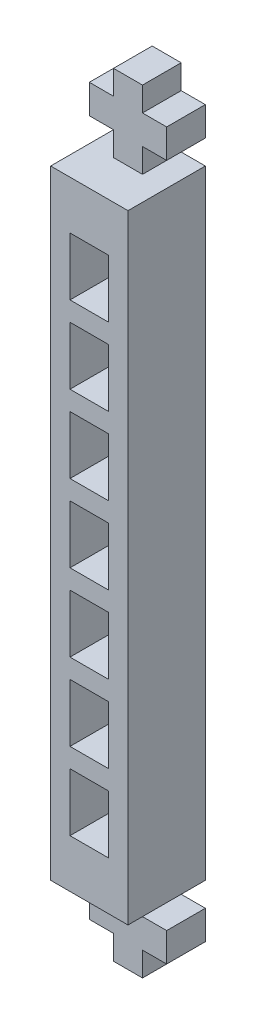
SolidWorks part; units mm, degrees
ref_plane "Front Plane" through (0, 0, 0) normal (0, 0, 1) x (1, 0, 0)
ref_plane "Top Plane" through (0, 0, 0) normal (0, 1, 0) x (1, 0, 0)
ref_plane "Right Plane" through (0, 0, 0) normal (1, 0, 0) x (0, 0, -1)
sketch "Sketch1" plane through (0, 0, 0) normal (0, 1, 0) x (1, 0, 0)
  line L1 (0, 0) -> (20, 0)
  line L2 (0, 0) -> (0, 20)
  line L3 (0, 20) -> (20, 20)
  line L4 (20, 0) -> (20, 20)
  dimension "D1" = 20
  dimension "D2" = 20
extrude "Boss-Extrude1" add sketch "Sketch1" along normal blind 200
sketch "Sketch2" plane through (20, 0, 0) normal (1, 0, 0) x (0, 0, -1)
  line L1 (0, 200) -> (10, 200)
  line L2 (0, 200) -> (0, 180)
  line L3 (0, 180) -> (10, 180)
  line L4 (10, 200) -> (10, 180)
  line L5 (0, 0) -> (10, 0)
  line L6 (0, 0) -> (0, 20)
  line L7 (0, 20) -> (10, 20)
  line L8 (10, 0) -> (10, 20)
  dimension "D1" = 20
  dimension "D2" = 10
  dimension "D3" = 20
  dimension "D4" = 10
extrude "Cut-Extrude1" cut sketch "Sketch2" against normal through all
sketch "Sketch3" plane through (0, 0, -20) normal (0, 0, -1) x (-1, 0, 0)
  line L1 (-20, 200) -> (0, 200)
  line L2 (-20, 200) -> (-20, 180)
  line L3 (-20, 180) -> (0, 180)
  line L4 (0, 200) -> (0, 180)
  line L5 (-20, 200) -> (-13.75, 200)
  line L6 (-20, 200) -> (-20, 193.75)
  line L7 (-20, 193.75) -> (-13.75, 193.75)
  line L8 (-13.75, 200) -> (-13.75, 193.75)
  line L9 (0, 200) -> (-6.25, 200)
  line L10 (0, 200) -> (0, 193.75)
  line L11 (0, 193.75) -> (-6.25, 193.75)
  line L12 (-6.25, 200) -> (-6.25, 193.75)
  line L13 (0, 180) -> (-6.25, 180)
  line L14 (0, 180) -> (0, 186.25)
  line L15 (0, 186.25) -> (-6.25, 186.25)
  line L16 (-6.25, 180) -> (-6.25, 186.25)
  line L17 (-20, 180) -> (-13.75, 180)
  line L18 (-20, 180) -> (-20, 186.25)
  line L19 (-20, 186.25) -> (-13.75, 186.25)
  line L20 (-13.75, 180) -> (-13.75, 186.25)
  line M22 (0, 0) -> (0, 200)
  line M23 (0, 200) -> (-20, 200)
  line M24 (-20, 200) -> (-20, 0)
  dimension "D1" = 20
  dimension "D2" = 20
  dimension "D3" = 6.25
extrude "Cut-Extrude2" cut sketch "Sketch3" against normal through all contours L12 L11 L4 M23 | L8 L1 L7 M24 | L3 L20 L19 M24 | L16 L3 L15 M22
sketch "Sketch4" plane through (0, 0, -20) normal (0, 0, -1) x (-1, 0, 0)
  line L0 (0, 180) -> (0, 0) construction
  line L1 (-20, 0) -> (0, 0)
  line L2 (-20, 0) -> (-20, 20)
  line L3 (-20, 20) -> (0, 20)
  line L4 (0, 0) -> (0, 20)
  line L6 (-20, 0) -> (-13.75, 0)
  line L7 (-20, 0) -> (-20, 6.25)
  line L8 (-20, 6.25) -> (-13.75, 6.25)
  line L9 (-13.75, 0) -> (-13.75, 6.25)
  line L10 (-20, 20) -> (-13.75, 20)
  line L11 (-20, 20) -> (-20, 13.75)
  line L12 (-20, 13.75) -> (-13.75, 13.75)
  line L13 (-13.75, 20) -> (-13.75, 13.75)
  line L14 (0, 20) -> (-6.25, 20)
  line L15 (0, 20) -> (0, 13.75)
  line L16 (0, 13.75) -> (-6.25, 13.75)
  line L17 (-6.25, 20) -> (-6.25, 13.75)
  line L18 (0, 0) -> (-6.25, 0)
  line L19 (0, 0) -> (0, 6.25)
  line L20 (0, 6.25) -> (-6.25, 6.25)
  line L21 (-6.25, 0) -> (-6.25, 6.25)
  line M33 (-20, 180) -> (-20, 0)
  line M34 (-20, 0) -> (0, 0)
  line M35 (0, 0) -> (0, 180)
  dimension "D1" = 20
  dimension "D2" = 6.25
extrude "Cut-Extrude3" cut sketch "Sketch4" against normal through all contours L13 L3 L12 M33 | L9 L8 L2 M34 | L3 L17 L16 L4 | L21 L20 M34 M35
sketch "Sketch5" plane through (0, 0, 0) normal (0, 0, 1) x (1, 0, 0)
  line L0 (0, 20) -> (20, 20) construction
  line L1 (5, 47.5) -> (15, 47.5)
  line L2 (5, 47.5) -> (5, 32.5)
  line L3 (5, 32.5) -> (15, 32.5)
  line L4 (15, 47.5) -> (15, 32.5)
  line L5 (20, 180) -> (20, 20) construction
  line L6 (5, 67.5) -> (5, 52.5)
  line L7 (5, 67.5) -> (15, 67.5)
  line L8 (15, 67.5) -> (15, 52.5)
  line L9 (5, 52.5) -> (15, 52.5)
  line L10 (5, 87.5) -> (5, 72.5)
  line L11 (5, 87.5) -> (15, 87.5)
  line L12 (15, 87.5) -> (15, 72.5)
  line L13 (5, 72.5) -> (15, 72.5)
  line L14 (5, 107.5) -> (5, 92.5)
  line L15 (5, 107.5) -> (15, 107.5)
  line L16 (15, 107.5) -> (15, 92.5)
  line L17 (5, 92.5) -> (15, 92.5)
  line L18 (5, 127.5) -> (5, 112.5)
  line L19 (5, 127.5) -> (15, 127.5)
  line L20 (15, 127.5) -> (15, 112.5)
  line L21 (5, 112.5) -> (15, 112.5)
  line L22 (5, 147.5) -> (5, 132.5)
  line L23 (5, 147.5) -> (15, 147.5)
  line L24 (15, 147.5) -> (15, 132.5)
  line L25 (5, 132.5) -> (15, 132.5)
  line L26 (5, 167.5) -> (5, 152.5)
  line L27 (5, 167.5) -> (15, 167.5)
  line L28 (15, 167.5) -> (15, 152.5)
  line L29 (5, 152.5) -> (15, 152.5)
  dimension "D1" = 10
  dimension "D2" = 15
  dimension "D3" = 12.5
  dimension "D4" = 5
  dimension "D5" = 7
extrude "Cut-Extrude4" cut sketch "Sketch5" against normal through all
